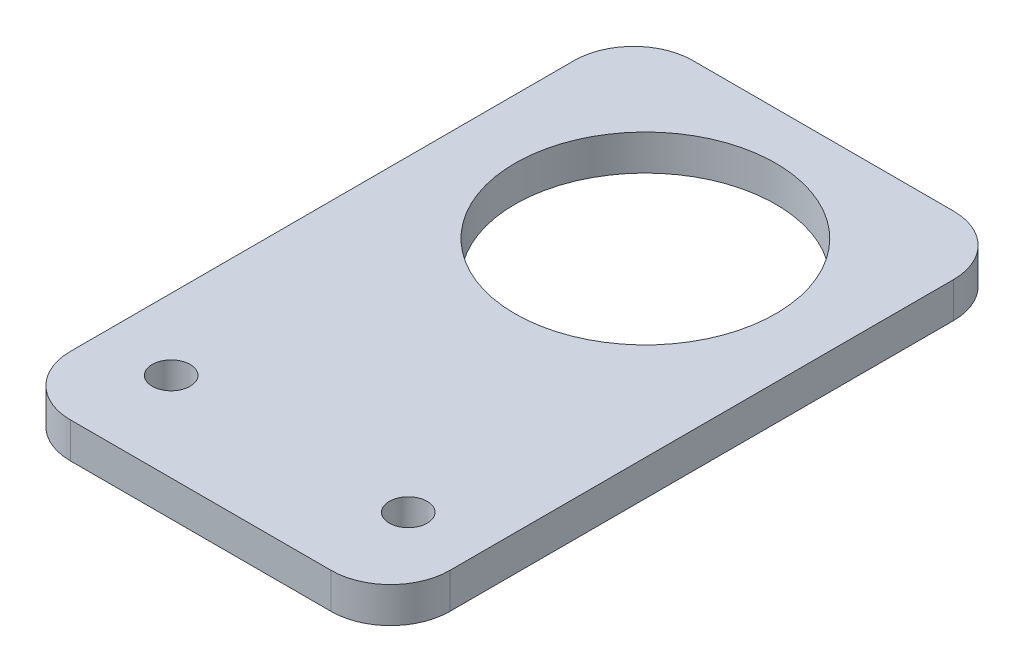
SolidWorks part; units mm, degrees
material "Carbon Fiber"
ref_plane "Front Plane" through (0, 0, 0) normal (0, 0, 1) x (1, 0, 0)
ref_plane "Top Plane" through (0, 0, 0) normal (0, 1, 0) x (1, 0, 0)
ref_plane "Right Plane" through (0, 0, 0) normal (1, 0, 0) x (0, 0, -1)
sketch "Sketch1" plane through (0, 0, 0) normal (0, 1, 0) x (1, 0, 0)
  line L0 (16, 52.5) -> (16, 0) construction
  line L1 (0, 0) -> (32, 0)
  line L2 (0, 0) -> (0, 52.5)
  line L3 (0, 52.5) -> (32, 52.5)
  line L4 (32, 0) -> (32, 52.5)
  line L5 (32, 7.5) -> (0, 7.5) construction
  circle A0 centre (16, 37.5) radius 11
  circle A1 centre (6, 7.5) radius 1.6
  circle A2 centre (26, 7.5) radius 1.6
  dimension "D1" = 22
  dimension "D2" = 15
  dimension "D3" = 20
  dimension "D4" = 30
  dimension "D6" = 6
  dimension "D7" = 3.2
  dimension "D5" = 7.5
extrude "Boss-Extrude1" add sketch "Sketch1" along normal blind 3
fillet "Fillet1" radius 5 4 edges at (0, 1.5, -52.5) (32, 1.5, -52.5) (0, 1.5, 0) (32, 1.5, 0)
